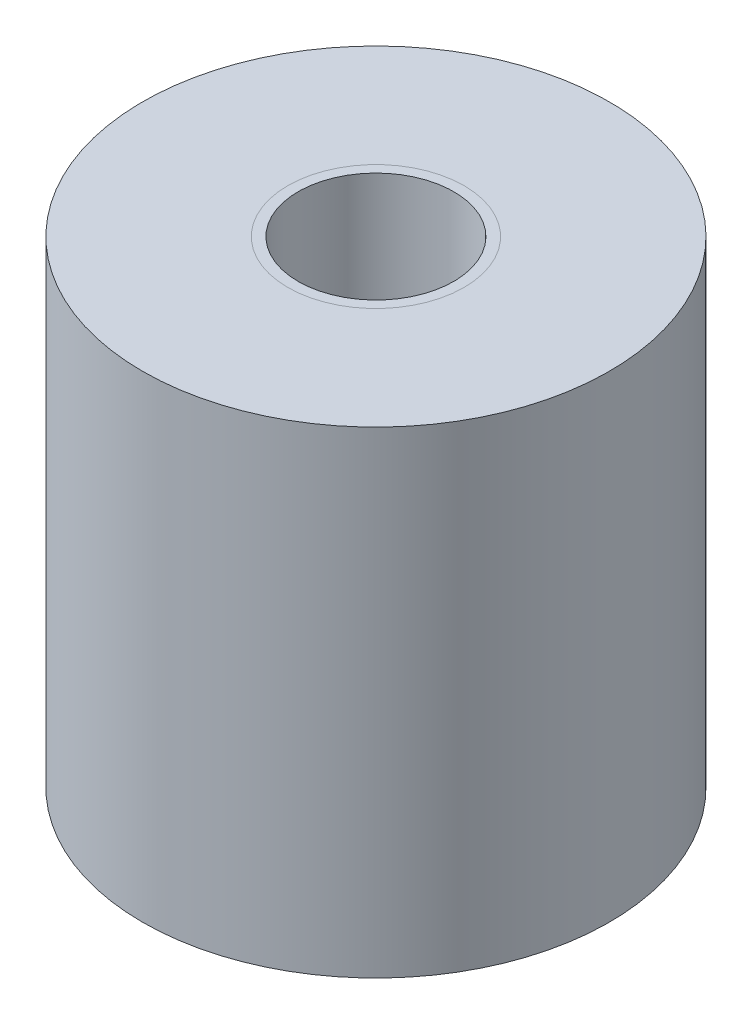
SolidWorks part; units mm, degrees
ref_plane "Front Plane" through (0, 0, 0) normal (0, 0, 1) x (1, 0, 0)
ref_plane "Top Plane" through (0, 0, 0) normal (0, 1, 0) x (1, 0, 0)
ref_plane "Right Plane" through (0, 0, 0) normal (1, 0, 0) x (0, 0, -1)
sketch "Sketch1" plane through (0, 0, 0) normal (0, 1, 0) x (1, 0, 0)
  circle A0 centre (0, 0) radius 19.05
  circle A1 centre (0, 0) radius 57.15
  dimension "D1" = 38.1
  dimension "D2" = 114.3
extrude "Boss-Extrude1" add sketch "Sketch1" along normal blind 116.84
sketch "Sketch2" plane through (0, 116.84, 0) normal (0, 1, 0) x (1, 0, 0)
  circle A0 centre (0, 0) radius 21.59
  circle A1 centre (0, 0) radius 19.05 construction
  dimension "D1" = 2.54
split line "Split Line1"
